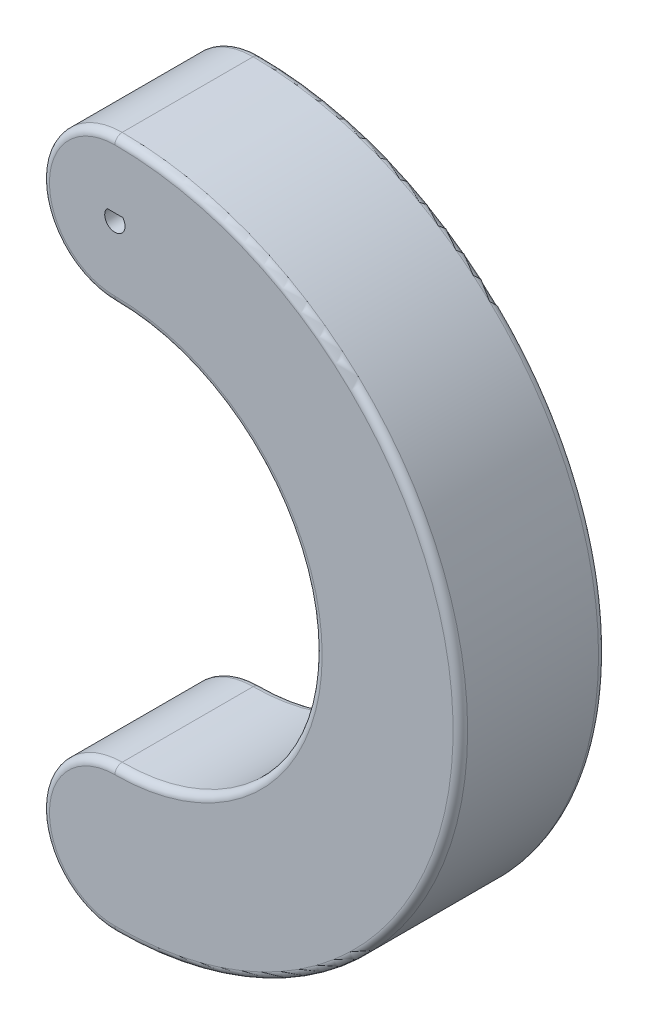
SolidWorks part; units mm, degrees
ref_plane "Front Plane" through (0, 0, 0) normal (0, 0, 1) x (1, 0, 0)
ref_plane "Top Plane" through (0, 0, 0) normal (0, 1, 0) x (1, 0, 0)
ref_plane "Right Plane" through (0, 0, 0) normal (1, 0, 0) x (0, 0, -1)
sketch "Sketch1" plane through (0, 0, 0) normal (0, 0, 1) x (1, 0, 0)
  line L0 (-1.118, 1.635) -> (1.118, 1.635) construction
  line L1 (0, 0.635) -> (0, -74.365) construction
  line L2 (-1.0724, 1.535) -> (1.0724, 1.535)
  arc A0 (-1.118, 1.635) -> (1.118, 1.635) centre (0, 0.635) ccw construction
  arc A1 (-1.118, 1.635) -> (1.118, 1.635) centre (0, 0.635) ccw construction
  circle A2 centre (0, 0.635) radius 10
  arc A3 (0, 0.635) -> (0, -74.365) centre (0, -36.865) cw construction
  arc A4 (0, -9.365) -> (0, -64.365) centre (0, -36.865) cw
  arc A5 (0, 10.635) -> (0, -84.365) centre (0, -36.865) cw
  arc A6 (0, -64.365) -> (0, -84.365) centre (0, -74.365) ccw
  arc A7 (-1.0724, 1.535) -> (1.0724, 1.535) centre (0, 0.635) ccw
  point P15 (0, 0)
  dimension "D1" = 20
  dimension "D2" = 75
extrude "Boss-Extrude1" add sketch "Sketch1" along normal blind 20 contours A2 A1 L0 | A4 A6 A5 A2
fillet "Fillet1" radius 1 8 edges at (-10, 0.635, 0) (27.5, -36.865, 0) (-10, -74.365, 0) (-10, 0.635, 20) (27.5, -36.865, 20) (-10, -74.365, 20) (47.5, -36.865, 0) (47.5, -36.865, 20)
